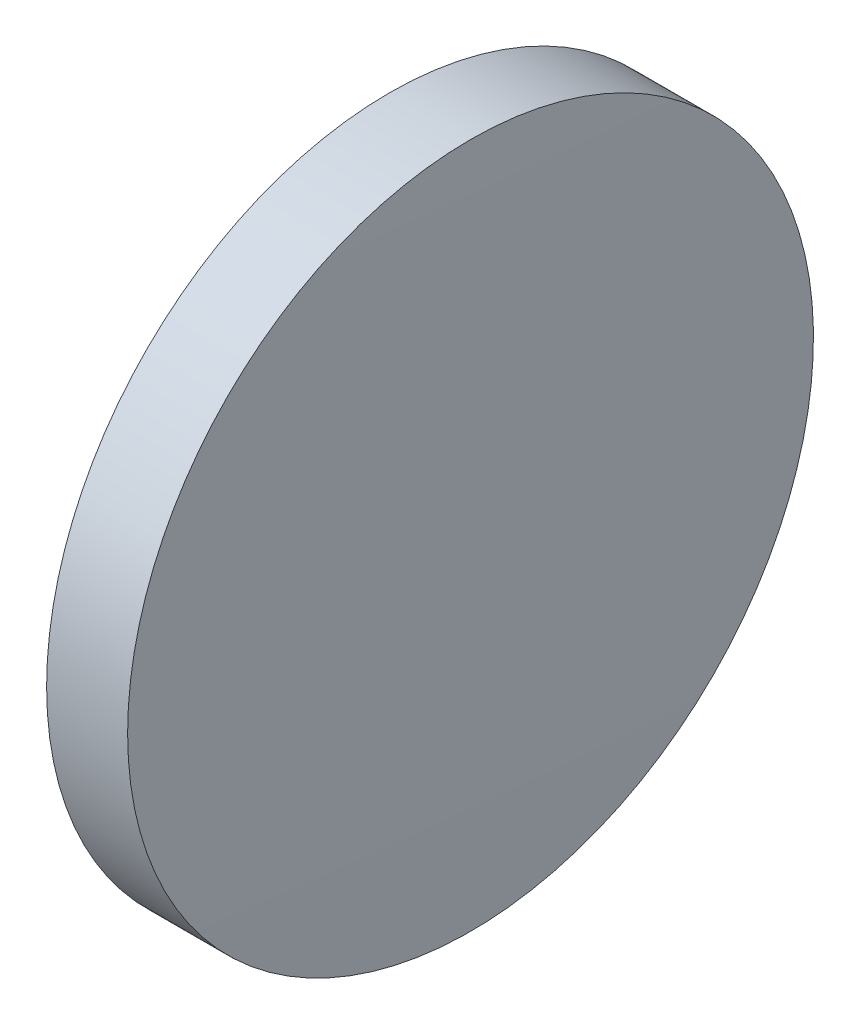
SolidWorks part; units mm, degrees
ref_plane "前视基准面" through (0, 0, 0) normal (0, 0, 1) x (1, 0, 0)
ref_plane "上视基准面" through (0, 0, 0) normal (0, 1, 0) x (1, 0, 0)
ref_plane "右视基准面" through (0, 0, 0) normal (1, 0, 0) x (0, 0, -1)
sketch "草图1" plane through (0, 0, 0) normal (0, 0, 1) x (1, 0, 0)
  line L0 (83.372, 48.6161) -> (89.8656, 48.6161) construction
  line L1 (84.9582, 61.3161) -> (87.9582, 61.3161)
  line L2 (87.9582, 61.3161) -> (87.9582, 35.9161)
  line L3 (87.9582, 35.9161) -> (84.9582, 35.9161)
  line L4 (84.9582, 35.9161) -> (84.9582, 61.3161)
  arc A0 (84.9582, 61.3161) -> (84.9582, 35.9161) centre (817.9177, 48.6161) ccw
  arc A1 (87.9582, 35.9161) -> (87.9582, 61.3161) centre (-645.0013, 48.6161) ccw
  dimension "D1" = 25.4
  dimension "D2" = 3
revolve "旋转1" add sketch "草图1" angle 360 about L0
